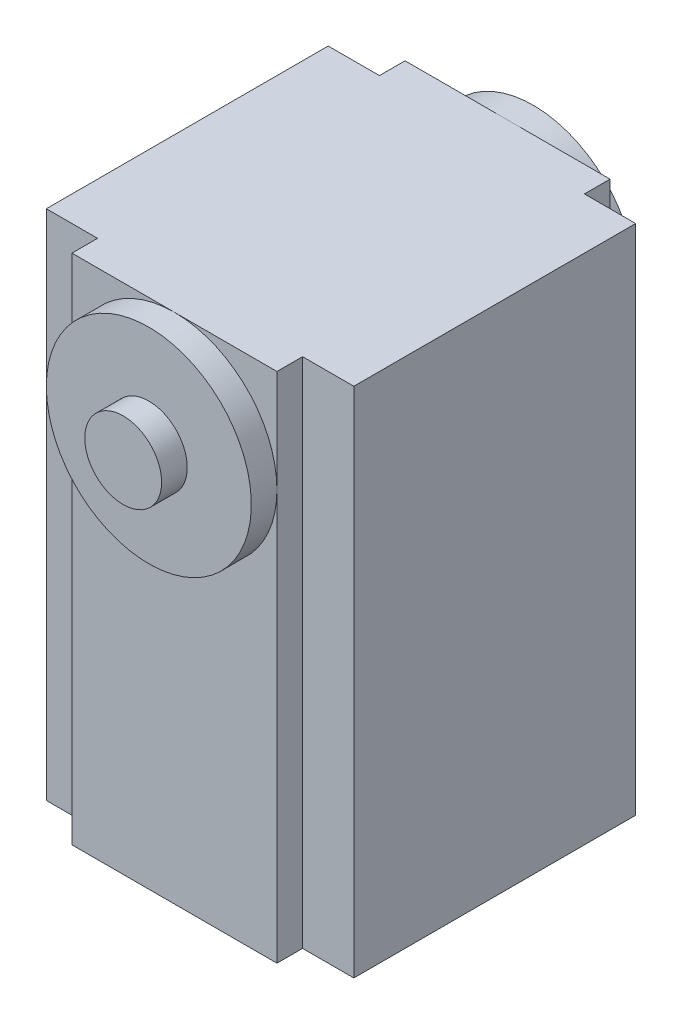
SolidWorks part; units mm, degrees
ref_plane "Front Plane" through (0, 0, 0) normal (0, 0, 1) x (1, 0, 0)
ref_plane "Top Plane" through (0, 0, 0) normal (0, 1, 0) x (1, 0, 0)
ref_plane "Right Plane" through (0, 0, 0) normal (1, 0, 0) x (0, 0, -1)
sketch "Sketch1" plane through (0, 0, 0) normal (0, 0, 1) x (1, 0, 0)
  line L1 (19.05, -31.75) -> (-19.05, -31.75)
  line L2 (19.05, -31.75) -> (19.05, 31.75)
  line L3 (19.05, 31.75) -> (-19.05, 31.75)
  line L4 (-19.05, -31.75) -> (-19.05, 31.75)
  line L5 (19.05, -31.75) -> (-19.05, 31.75) construction
  line L6 (19.05, 31.75) -> (-19.05, -31.75) construction
  point P0 (0, 0)
  dimension "D1" = 63.5
  dimension "D2" = 38.1
extrude "Boss-Extrude1" add sketch "Sketch1" along normal blind 41.275
sketch "Sketch2" plane through (0, 0, 0) normal (0, 0, -1) x (-1, 0, 0)
  line L0 (0, 31.75) -> (0, -31.75) construction
  line L1 (-19.05, 31.75) -> (19.05, 31.75) construction
  line L2 (19.05, -31.75) -> (-19.05, -31.75) construction
  circle A0 centre (0, 19.05) radius 12.7
  dimension "D1" = 25.4
extrude "Boss-Extrude2" add sketch "Sketch2" along normal blind 3.175
sketch "Sketch3" plane through (0, 0, -3.175) normal (0, 0, -1) x (-1, 0, 0)
  line L0 (0, 31.75) -> (0, 6.35) construction
  line L1 (-19.05, 31.75) -> (19.05, 31.75) construction
  circle A0 centre (0, 19.05) radius 4.7625
  circle A1 centre (0, 19.05) radius 12.7 construction
  point P11 (0, 19.05)
  dimension "D1" = 9.525
extrude "Boss-Extrude3" add sketch "Sketch3" along normal blind 3.175
ref_plane "Plane1" through (0, 0, 20.6375) normal (0, 0, -1) x (-1, 0, 0)
mirror "Mirror1" about plane through (0, 0, 20.6375) normal (0, 0, -1) of "Boss-Extrude2", "Boss-Extrude3"
sketch "Sketch5" plane through (0, 0, 41.275) normal (0, 0, 1) x (1, 0, 0)
  line L0 (19.05, -31.75) -> (-19.05, -31.75) construction
  line L1 (-19.05, 31.75) -> (-12.7, 31.75)
  line L2 (-19.05, 31.75) -> (-19.05, -31.75)
  line L3 (-19.05, -31.75) -> (-12.7, -31.75)
  line L4 (-12.7, 31.75) -> (-12.7, -31.75)
  line L6 (19.05, 31.75) -> (12.7, 31.75)
  line L7 (19.05, 31.75) -> (19.05, -31.75)
  line L8 (19.05, -31.75) -> (12.7, -31.75)
  line L9 (12.7, 31.75) -> (12.7, -31.75)
  dimension "D1" = 6.35
  dimension "D2" = 6.35
extrude "Cut-Extrude1" cut sketch "Sketch5" against normal blind 3.175
mirror "Mirror2" about plane through (0, 0, 20.6375) normal (0, 0, -1) of "Cut-Extrude1"
